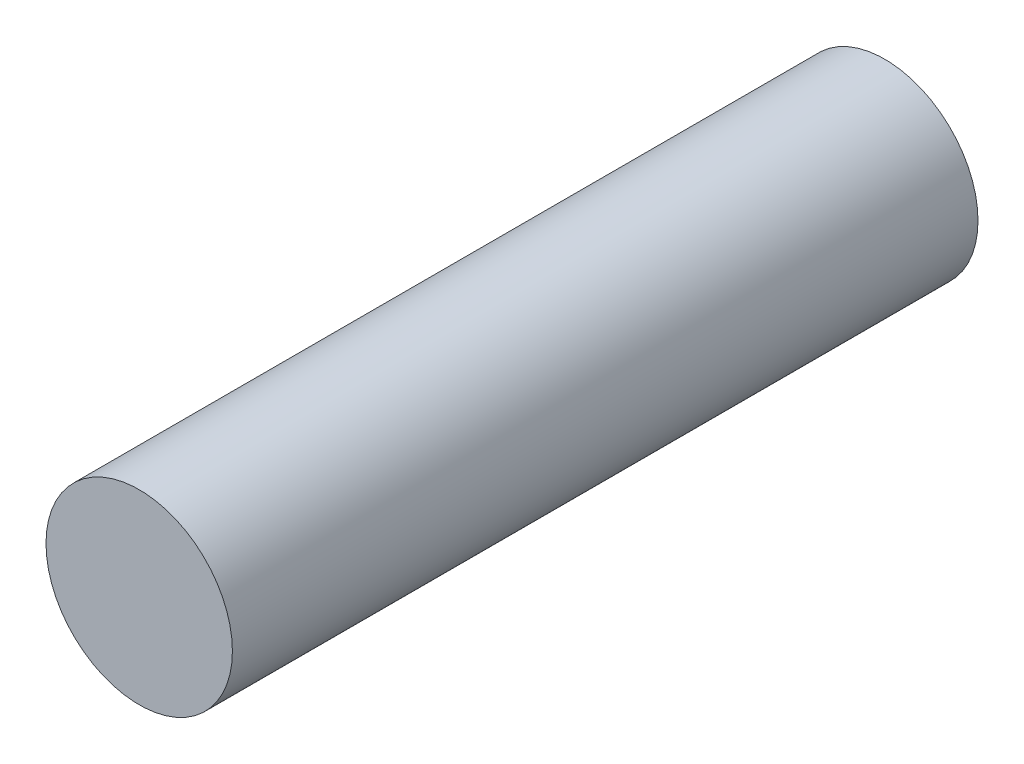
SolidWorks part; units mm, degrees
ref_plane "Front Plane" through (0, 0, 0) normal (0, 0, 1) x (1, 0, 0)
ref_plane "Top Plane" through (0, 0, 0) normal (0, 1, 0) x (1, 0, 0)
ref_plane "Right Plane" through (0, 0, 0) normal (1, 0, 0) x (0, 0, -1)
sketch "Sketch1" plane through (0, 0, 0) normal (0, 0, 1) x (1, 0, 0)
  circle A0 centre (0, 0) radius 10
extrude "Boss-Extrude1" add sketch "Sketch1" along normal blind 80
